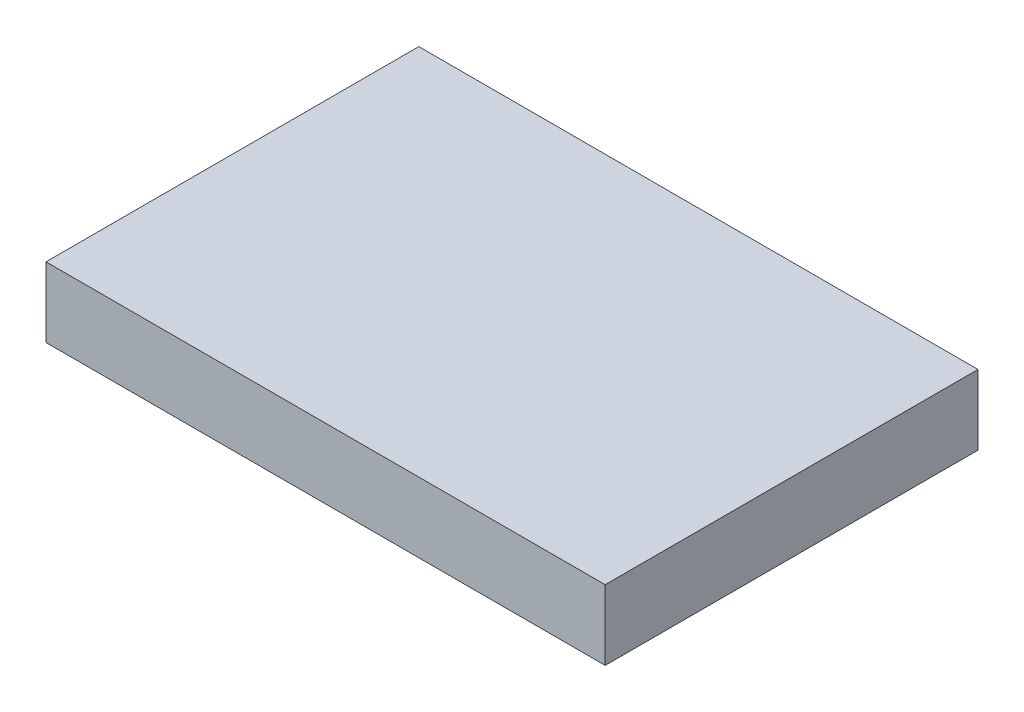
SolidWorks part; units mm, degrees
ref_plane "Plan de face" through (0, 0, 0) normal (0, 0, 1) x (1, 0, 0)
ref_plane "Plan de dessus" through (0, 0, 0) normal (0, 1, 0) x (1, 0, 0)
ref_plane "Plan de droite" through (0, 0, 0) normal (1, 0, 0) x (0, 0, -1)
sketch "Esquisse2" plane through (0, 0, 0) normal (0, 1, 0) x (1, 0, 0)
  line L1 (0, 0) -> (24, 0)
  line L2 (0, 0) -> (0, 16)
  line L3 (0, 16) -> (24, 16)
  line L4 (24, 0) -> (24, 16)
  dimension "D1" = 24
  dimension "D2" = 16
extrude "Boss.-Extru.1" add sketch "Esquisse2" along normal blind 3
